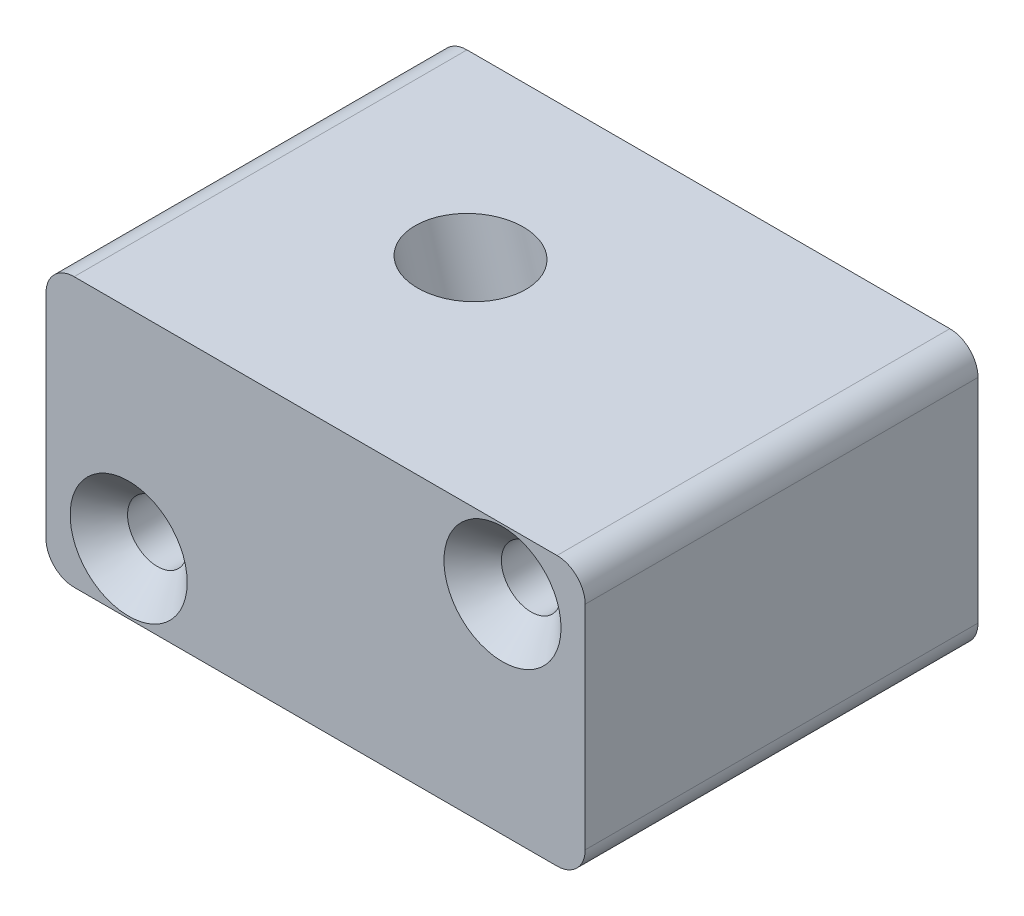
SolidWorks part; units mm, degrees
material "6061 Alloy"
ref_plane "Top Plane" through (0, 0, 0) normal (0, 0, 1) x (1, 0, 0)
ref_plane "Front Plane" through (0, 0, 0) normal (0, 1, 0) x (1, 0, 0)
ref_plane "Right Plane" through (0, 0, 0) normal (1, 0, 0) x (0, 0, -1)
sketch "Sketch1" plane through (0, 0, 0) normal (0, 0, 1) x (1, 0, 0)
  line L1 (-21.45, -11.95) -> (21.45, -11.95)
  line L2 (-23.95, -9.45) -> (-23.95, 9.45)
  line L3 (-21.45, 11.95) -> (21.45, 11.95)
  line L4 (23.95, -9.45) -> (23.95, 9.45)
  line L5 (-23.95, -11.95) -> (23.95, 11.95) construction
  line L6 (-23.95, 11.95) -> (23.95, -11.95) construction
  arc A0 (-23.95, -9.45) -> (-21.45, -11.95) centre (-21.45, -9.45) ccw
  arc A1 (21.45, -11.95) -> (23.95, -9.45) centre (21.45, -9.45) ccw
  arc A2 (23.95, 9.45) -> (21.45, 11.95) centre (21.45, 9.45) ccw
  arc A3 (-21.45, 11.95) -> (-23.95, 9.45) centre (-21.45, 9.45) ccw
  point P0 (0, 0)
  dimension "D3" = 2.5
  dimension "D1" = 47.9
  dimension "D2" = 23.9
extrude "Boss-Extrude1" add sketch "Sketch1" along normal mid plane 34.9
sketch "Sketch11" plane through (0, 0, 0) normal (0, 0, 1) x (1, 0, 0)
  line L0 (-3.8776, 11.95) -> (3.8555, -11.95)
  line L1 (21.45, 11.95) -> (-21.45, 11.95) construction
  line L2 (0, 11.95) -> (0, -11.95) construction
  line L3 (-21.45, -11.95) -> (21.45, -11.95) construction
sketch "Sketch12" plane through (0, 11.95, 0) normal (0, 1, 0) x (1, 0, 0)
  line L0 (-3.8776, 0) -> (3.8555, 0) construction
  circle A0 centre (-3.0877, 0) radius 4.7714
  dimension "D1" = 9.5428
sweep "Cut-Sweep1" [suppressed] cut profiles "Sketch12" path "Sketch11"
sketch "Sketch15" plane through (0, 0, 17.45) normal (0, 0, 1) x (1, 0, 0)
  line L0 (-23.95, -9.45) -> (23.95, 9.45) construction
  line L9 (-21.45, -11.95) -> (0, 11.95) construction
  line L10 (21.45, 11.95) -> (-21.45, 11.95) construction
  line L12 (21.45, 11.95) -> (0, -11.95) construction
  line L13 (-21.45, -11.95) -> (21.45, -11.95) construction
  point P0 (-16.6054, -6.552)
  point P2 (16.6054, 6.552)
hole_wizard "CSK for M5 Flat Head Machine Screw1" positions "Sketch15" profile "Sketch14" countersink size "M5" standard "ANSI Metric" end condition through all
sketch "Sketch14" plane through (-16.6054, -6.552, 17.45) normal (1, 0, 0) x (0, -1, 0)
  line L0 (0, 0) -> (0, 34.9)
  line L1 (0, 34.9) -> (2.65, 34.9)
  line L2 (2.65, 34.9) -> (2.65, 2.55)
  line L3 (2.65, 2.55) -> (5.2, 0)
  line L5 (5.2, 0) -> (0, 0)
  line L6 (-2.65, 2.55) -> (-5.2, 0) construction
  line L11 (0, -6.35) -> (0, 107.95) construction
  dimension "Thru Hole Dia." = 5.3
  dimension "Thru Hole Depth" = 34.9
  dimension "Near C'Sink Dia." = 10.4
  dimension "Near C'Sink Angle" = 90
ref_plane "Plane4" through (-2.6422, -0.8078, 0) normal (0.9563, 0.2924, 0) x (0, 0, -1)
sketch "Sketch21" [suppressed] plane through (-2.7626, -0.8976, 0) normal (0.9511, 0.309, 0) x (0, 0, -1)
  line L2 (-2.1354, -40.7451) -> (0, 0)
  line L3 (0, 0) -> (1.9625, 37.4468)
  line L4 (-2.1354, -40.7451) -> (2.0556, -40.9647)
  line L5 (2.0556, -40.9647) -> (6.1648, 37.4419)
  line L6 (1.9625, 37.4468) -> (6.1648, 37.4419)
  point P2 (0, 0)
  dimension "D1" = 4.191
revolve "Cut-Revolve1" [suppressed] cut sketch "Sketch21" angle 360 about L3
ref_plane "Plane5" through (-1.5185, -0.4643, 0) normal (0.9563, 0.2924, 0) x (0, 0, -1)
sketch "Sketch24" plane through (-1.5185, -0.4643, 0) normal (0.9563, 0.2924, 0) x (0, 0, -1)
  line L4 (1.63, 21.7584) -> (1.63, -21.8488)
  line L5 (1.63, -21.8488) -> (6.329, -21.8488)
  line L6 (6.329, -21.8488) -> (6.329, 21.7584)
  line L7 (6.329, 21.7584) -> (1.63, 21.7584)
  line L8 (-17.45, 5.1565) -> (-17.45, 17.6992) construction
  line L9 (-17.45, 5.1565) -> (17.45, 5.1565) construction
  dimension "D1" = 4.699
  dimension "D2" = 19.08
  dimension "D3" = 16.602
revolve "Cut-Revolve2" cut sketch "Sketch24" angle 360 about L4
